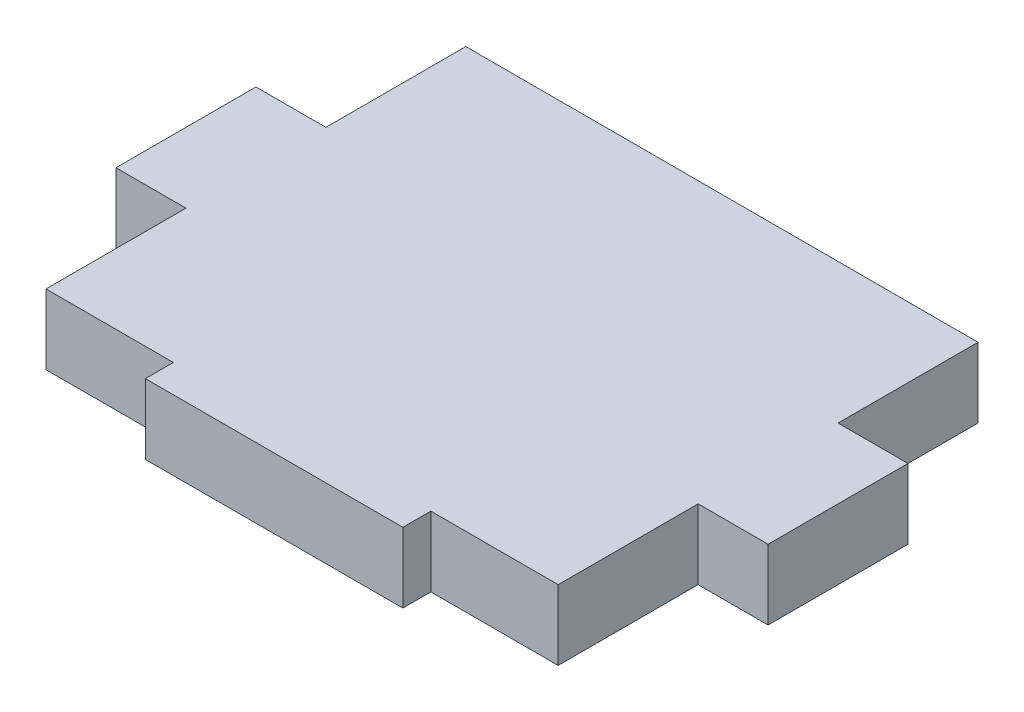
SolidWorks part; units mm, degrees
ref_plane "Front Plane" through (0, 0, 0) normal (0, 0, 1) x (1, 0, 0)
ref_plane "Top Plane" through (0, 0, 0) normal (0, 1, 0) x (1, 0, 0)
ref_plane "Right Plane" through (0, 0, 0) normal (1, 0, 0) x (0, 0, -1)
sketch "Sketch1" plane through (0, 0, 0) normal (0, 1, 0) x (1, 0, 0)
  line L1 (-23.241, -19.05) -> (23.241, -19.05)
  line L2 (-23.241, -19.05) -> (-23.241, 19.05)
  line L3 (-23.241, 19.05) -> (23.241, 19.05)
  line L4 (23.241, -19.05) -> (23.241, 19.05)
  line L5 (-23.241, -19.05) -> (23.241, 19.05) construction
  line L6 (-23.241, 19.05) -> (23.241, -19.05) construction
  point P0 (0, 0)
  dimension "D1" = 38.1
  dimension "D2" = 46.482
extrude "Boss-Extrude1" add sketch "Sketch1" along normal mid plane 6.35
sketch "Sketch2" plane through (0, 3.175, 0) normal (0, 1, 0) x (1, 0, 0)
  line L0 (-23.241, -19.05) -> (23.241, -19.05) construction
  line L1 (-11.684, -19.05) -> (11.684, -19.05)
  line L2 (-11.684, -19.05) -> (-11.684, -21.59)
  line L3 (-11.684, -21.59) -> (11.684, -21.59)
  line L4 (11.684, -19.05) -> (11.684, -21.59)
  line L5 (-29.591, -6.35) -> (-29.591, -19.05) construction
  line L6 (11.684, -19.05) -> (29.591, -19.05) construction
  line L7 (-23.241, 19.05) -> (-23.241, -19.05) construction
  line L8 (-23.241, -6.35) -> (-29.591, -6.35)
  line L9 (-23.241, -6.35) -> (-23.241, 6.35)
  line L10 (-23.241, 6.35) -> (-29.591, 6.35)
  line L11 (-29.591, -6.35) -> (-29.591, 6.35)
  line L12 (-23.241, 19.05) -> (-23.241, 6.35) construction
  line L13 (-23.241, -6.35) -> (-23.241, -19.05) construction
  line L14 (0, 19.05) -> (0, -19.05) construction
  line L15 (23.241, 19.05) -> (-23.241, 19.05) construction
  line L16 (29.591, -6.35) -> (29.591, 6.35)
  line L17 (23.241, 6.35) -> (29.591, 6.35)
  line L18 (23.241, -6.35) -> (23.241, 6.35)
  line L19 (23.241, -6.35) -> (29.591, -6.35)
  line L20 (29.591, -19.05) -> (29.591, -6.35) construction
  line L21 (-29.591, -19.05) -> (-23.241, -19.05) construction
  dimension "D1" = 2.54
  dimension "D2" = 6.35
  dimension "D3" = 23.368
extrude "Boss-Extrude2" add sketch "Sketch2" against normal blind 6.35
equation "\"D1@Boss-Extrude1\"=\"material\""
equation "\"D1@Boss-Extrude2\"=\"material\""
equation "\"material\"=\"GMaterial@Platform.assembly\""
equation "\"D1@Sketch2\"=\"Acrylic\""
equation "\"D2@Sketch2\"=\"material\""
equation "\"Acrylic\"=\"Acrylic@Platform.assembly\""
